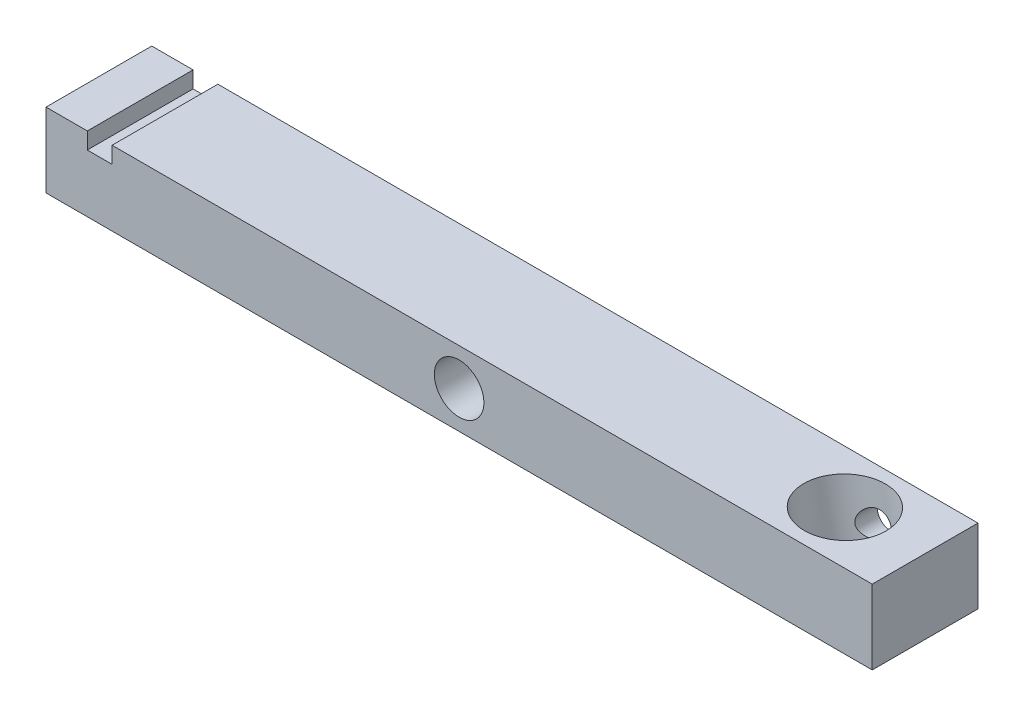
SolidWorks part; units mm, degrees
ref_plane "Front Plane" through (0, 0, 0) normal (0, 0, 1) x (1, 0, 0)
ref_plane "Top Plane" through (0, 0, 0) normal (0, 1, 0) x (1, 0, 0)
ref_plane "Right Plane" through (0, 0, 0) normal (1, 0, 0) x (0, 0, -1)
sketch "Sketch1" plane through (0, 0, 0) normal (0, 0, 1) x (1, 0, 0)
  line L1 (-63.5, -5.715) -> (63.5, -5.715)
  line L2 (-63.5, -5.715) -> (-63.5, 5.715)
  line L3 (-63.5, 5.715) -> (63.5, 5.715)
  line L4 (63.5, -5.715) -> (63.5, 5.715)
  line L5 (-63.5, -5.715) -> (63.5, 5.715) construction
  line L6 (-63.5, 5.715) -> (63.5, -5.715) construction
  point P0 (0, 0)
  dimension "D1" = 11.43
  dimension "D2" = 127
extrude "Boss-Extrude1" add sketch "Sketch1" along normal mid plane 16.256
sketch "Sketch6" plane through (0, 0, 8.128) normal (0, 0, 1) x (1, 0, 0)
  line L0 (-57.15, 5.715) -> (-57.15, 3.175)
  line L1 (43.18, -3.175) -> (43.18, -5.715)
  line L2 (-57.15, 3.175) -> (-53.34, 3.175)
  line L3 (-53.34, 3.175) -> (-53.34, 5.715)
  line L4 (-57.15, 5.715) -> (-53.34, 5.715)
  line L5 (63.5, 5.715) -> (-63.5, 5.715) construction
  line L6 (43.18, -5.715) -> (46.99, -5.715)
  line L7 (46.99, -5.715) -> (46.99, -3.175)
  line L8 (43.18, -3.175) -> (46.99, -3.175)
  line L9 (-63.5, -5.715) -> (63.5, -5.715) construction
  dimension "D4" = 2.54
  dimension "D1" = 53.34
  dimension "D2" = 2.54
  dimension "D3" = 57.15
  dimension "D5" = 43.18
  dimension "D6" = 3.81
extrude "Cut-Extrude1" cut sketch "Sketch6" against normal up to surface (16.256 mm away) contours L4 L3 L2 L0 up to face at (0, 0, -8.128)
sketch "Sketch12" plane through (0, 0, 8.128) normal (0, 0, 1) x (1, 0, 0)
  circle A0 centre (0, 0) radius 3.81
  dimension "D1" = 7.62
extrude "Cut-Extrude2" cut sketch "Sketch12" against normal up to surface (16.256 mm away) up to face at (-27.6225, 2.2225, -8.128)
ref_plane "Plane1" through (2.8921, -16.4018, 0) normal (0.1736, -0.9848, 0) x (0, 0, -1)
sketch "Sketch14" plane through (2.8921, -16.4018, 0) normal (0.1736, -0.9848, 0) x (0, 0, -1)
  line L0 (-8.128, 61.5429) -> (8.128, 61.5429) construction
  line L1 (0, -11.2201) -> (0, 68.737) construction
  circle A0 centre (0, 51.3829) radius 6.223
  dimension "D1" = 12.446
  dimension "D2" = 10.16
extrude "Cut-Extrude3" cut sketch "Sketch14" against normal blind 25.4
sketch "Sketch17" plane through (0, 0, -8.128) normal (0, 0, -1) x (-1, 0, 0)
  circle A0 centre (-50.0486, 0) radius 2.032
  dimension "D1" = 4.064
extrude "Cut-Extrude4" cut sketch "Sketch17" against normal up to surface (3.4429 mm away)
